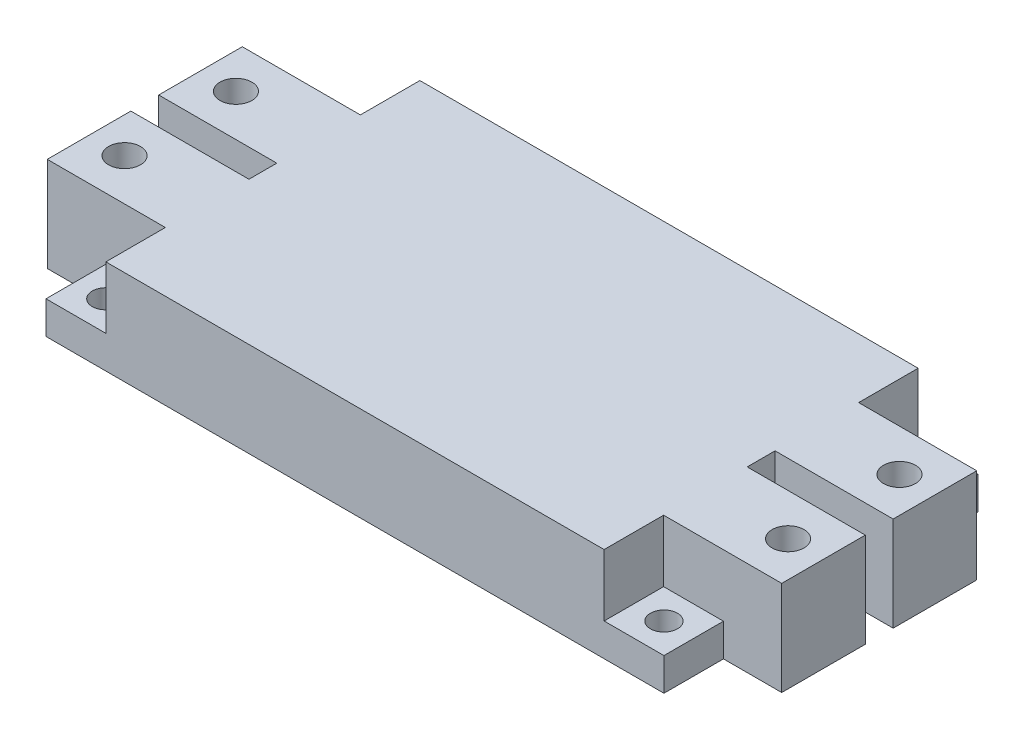
SolidWorks part; units mm, degrees
ref_plane "Front Plane" through (0, 0, 0) normal (0, 0, 1) x (1, 0, 0)
ref_plane "Top Plane" through (0, 0, 0) normal (0, 1, 0) x (1, 0, 0)
ref_plane "Right Plane" through (0, 0, 0) normal (1, 0, 0) x (0, 0, -1)
sketch "Sketch1" plane through (0, 0, 0) normal (0, 1, 0) x (1, 0, 0)
  line L0 (-55.095, -25.095) -> (-55.095, 25.09) construction
  line L1 (-61, 31) -> (61, 31)
  line L2 (-61, 31) -> (-61, -31)
  line L3 (-61, -31) -> (61, -31)
  line L4 (61, 31) -> (61, -31) construction
  line L5 (-61, 31) -> (61, -31) construction
  line L6 (-61, -31) -> (61, 31) construction
  line L7 (0, 31) -> (0, -31)
  circle A0 centre (-55.095, 25.09) radius 2.675
  circle A3 centre (-55.095, -25.095) radius 2.675
  point P0 (0, 0)
  dimension "D3" = 5.35
  dimension "D4" = 5.35
  dimension "D1" = 122
  dimension "D2" = 62
  dimension "D7" = 5.905
  dimension "D8" = 5.905
  dimension "D9" = 5.91
extrude "Base" add sketch "Sketch1" along normal blind 6.45 contours L7 L1 L2 L3 A3 A0
sketch "Sketch2" plane through (0, 6.45, 0) normal (0, 1, 0) x (1, 0, 0)
  line L1 (-49.185, 31) -> (0, 31)
  line L2 (-49.185, 31) -> (-49.185, -31)
  line L3 (-49.185, -31) -> (0, -31)
  line L4 (0, 31) -> (0, -31)
  line L7 (-61, -31) -> (0, -31) construction
  line L8 (0, 31) -> (0, -31) construction
  line L9 (-61, 31) -> (0, 31) construction
  circle A2 centre (-55.095, -25.095) radius 2.675 construction
  dimension "D1" = 5.91
extrude "Semiconductor" add sketch "Sketch2" along normal blind 12.22
sketch "Sketch3" plane through (0, 0, 0) normal (0, -1, 0) x (1, 0, 0)
  line L1 (-49.185, -19.25) -> (-72.5, -19.25)
  line L2 (-49.185, -19.25) -> (-49.185, -2.75)
  line L3 (-49.185, -2.75) -> (-72.5, -2.75)
  line L4 (-72.5, -19.25) -> (-72.5, -2.75)
  line L5 (-49.185, 2.75) -> (-49.185, -2.75) construction
  line L6 (-49.185, 2.75) -> (-72.5, 2.75)
  line L7 (-49.185, 2.75) -> (-49.185, 19.25)
  line L8 (-49.185, 19.25) -> (-72.5, 19.25)
  line L9 (-72.5, 2.75) -> (-72.5, 19.25)
  line L10 (-65.5, 11) -> (-65.5, -11) construction
  line L11 (-65.5, 11) -> (-49.185, 11) construction
  line L12 (-65.5, -11) -> (-49.185, -11) construction
  line L14 (-61, -31) -> (-61, 31) construction
  line L15 (-49.185, -31) -> (-49.185, 31) construction
  circle A0 centre (-65.5, -11) radius 3.15
  circle A1 centre (-65.5, 11) radius 3.15
  point P10 (-49.185, 0)
  dimension "D5" = 6.3
  dimension "D6" = 6.3
  dimension "D1" = 38.5
  dimension "D2" = 16.5
  dimension "D3" = 16.5
  dimension "D4" = 11.5
  dimension "D7" = 7
extrude "Tabs" add sketch "Sketch3" against normal up to surface (18.67 mm away)
mirror "Mirror" about plane through (0, 6.45, 0) normal (1, 0, 0) of bodies 103
